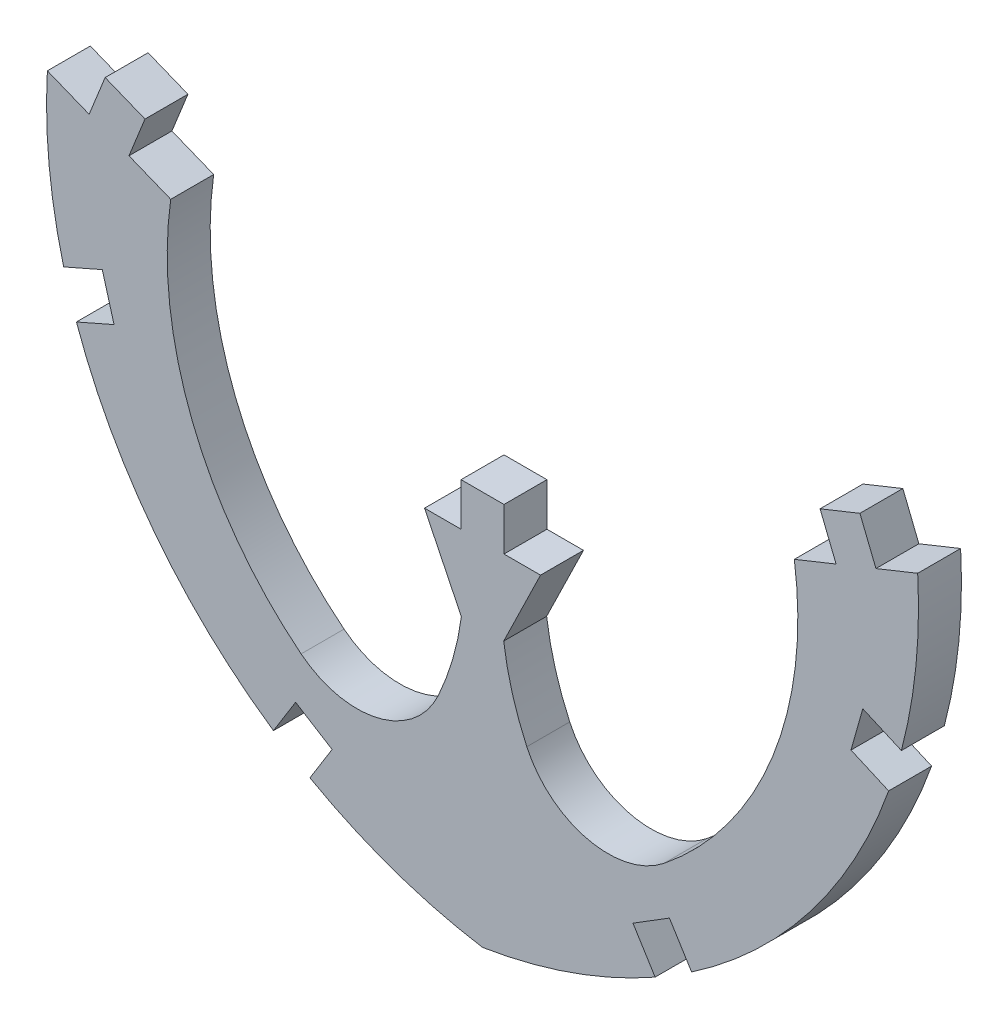
SolidWorks part; units mm, degrees
ref_plane "Front Plane" through (0, 0, 0) normal (0, 0, 1) x (1, 0, 0)
ref_plane "Top Plane" through (0, 0, 0) normal (0, 1, 0) x (1, 0, 0)
ref_plane "Right Plane" through (0, 0, 0) normal (1, 0, 0) x (0, 0, -1)
sketch "Sketch1" plane through (0, 0, 0) normal (0, 0, 1) x (1, 0, 0)
  line L0 (106.8113, -4.2056) -> (105.5039, -1.524)
  line L1 (101.4367, -11.8468) -> (102.2231, -10.5816)
  line L2 (92.1175, 5.2258) -> (93.5997, 4.6299)
  line L3 (121.0579, 0.0883) -> (120.6391, -1.3922)
  line L4 (105.5039, -1.524) -> (106.8002, -1.524)
  line L5 (106.8002, -1.524) -> (106.8002, 0)
  line L6 (106.8002, 0) -> (108.3242, 0)
  line L7 (108.3242, 0) -> (108.3242, -1.524)
  line L8 (107.5622, 0) -> (107.5622, 3.4656) construction
  line L9 (108.3242, -1.524) -> (108.3242, 0)
  line L10 (109.6204, -1.524) -> (108.3242, -1.524)
  line L11 (123.0068, 5.2258) -> (121.5246, 4.6299)
  line L12 (108.313, -4.2056) -> (109.6204, -1.524)
  line L13 (95.0137, 4.0615) -> (96.4959, 3.4656)
  line L14 (95.0137, 4.0615) -> (95.5822, 5.4755)
  line L15 (93.5997, 4.6299) -> (94.1682, 6.0439)
  line L16 (119.5421, 5.4755) -> (120.9562, 6.0439)
  line L17 (95.5822, 5.4755) -> (94.1682, 6.0439)
  line L18 (121.5246, 4.6299) -> (120.9562, 6.0439)
  line L19 (120.1106, 4.0615) -> (119.5421, 5.4755)
  line L20 (120.1106, 4.0615) -> (118.6284, 3.4656)
  line L21 (114.982, -11.0423) -> (114.1955, -9.777)
  line L22 (122.4281, -0.5128) -> (121.0579, 0.0883)
  line L23 (121.9756, -1.9785) -> (120.6391, -1.3922)
  line L24 (113.6876, -11.8468) -> (112.9012, -10.5816)
  line L25 (100.9288, -9.777) -> (102.2231, -10.5816)
  line L26 (114.1955, -9.777) -> (112.9012, -10.5816)
  line L27 (100.1423, -11.0423) -> (100.9288, -9.777)
  line L28 (93.1487, -1.9785) -> (94.4852, -1.3922)
  line L29 (92.6962, -0.5128) -> (94.0664, 0.0883)
  line L30 (94.0664, 0.0883) -> (94.4852, -1.3922)
  arc A0 (107.5622, -13.9966) -> (101.4367, -11.8468) centre (110.5019, 4.1812) cw
  arc A1 (96.4959, 3.4656) -> (101.1236, -8.1939) centre (109.0313, 1.6927) ccw
  arc A2 (106.8113, -4.2056) -> (105.991, -7.0419) centre (97.0032, -2.9055) cw
  arc A3 (105.991, -7.0419) -> (101.1236, -8.1939) centre (103.1067, -5.7145) cw
  arc A4 (109.1334, -7.0419) -> (114.0007, -8.1939) centre (112.0176, -5.7145) ccw
  arc A5 (108.313, -4.2056) -> (109.1334, -7.0419) centre (118.1211, -2.9055) ccw
  arc A6 (118.6284, 3.4656) -> (114.0007, -8.1939) centre (106.093, 1.6927) cw
  arc A7 (107.5622, -13.9966) -> (113.6876, -11.8468) centre (104.6224, 4.1812) ccw
  arc A8 (122.4281, -0.5128) -> (123.0068, 5.2258) centre (104.6224, 4.1812) ccw
  arc A9 (114.982, -11.0423) -> (121.9756, -1.9785) centre (104.6224, 4.1812) ccw
  arc A10 (100.1423, -11.0423) -> (93.1487, -1.9785) centre (110.5019, 4.1812) cw
  arc A11 (92.6962, -0.5128) -> (92.1175, 5.2258) centre (110.5019, 4.1812) cw
  dimension "D1" = 3.175
extrude "Boss-Extrude1" add sketch "Sketch1" along normal blind 1.524 contours A0 A7 L11 L18 L16 L19 L20 A6 A4 A5 L12 L10 L7 L6 L5 L4 L0 A2 A3 A1 L13 L14 L17 L15 L2
